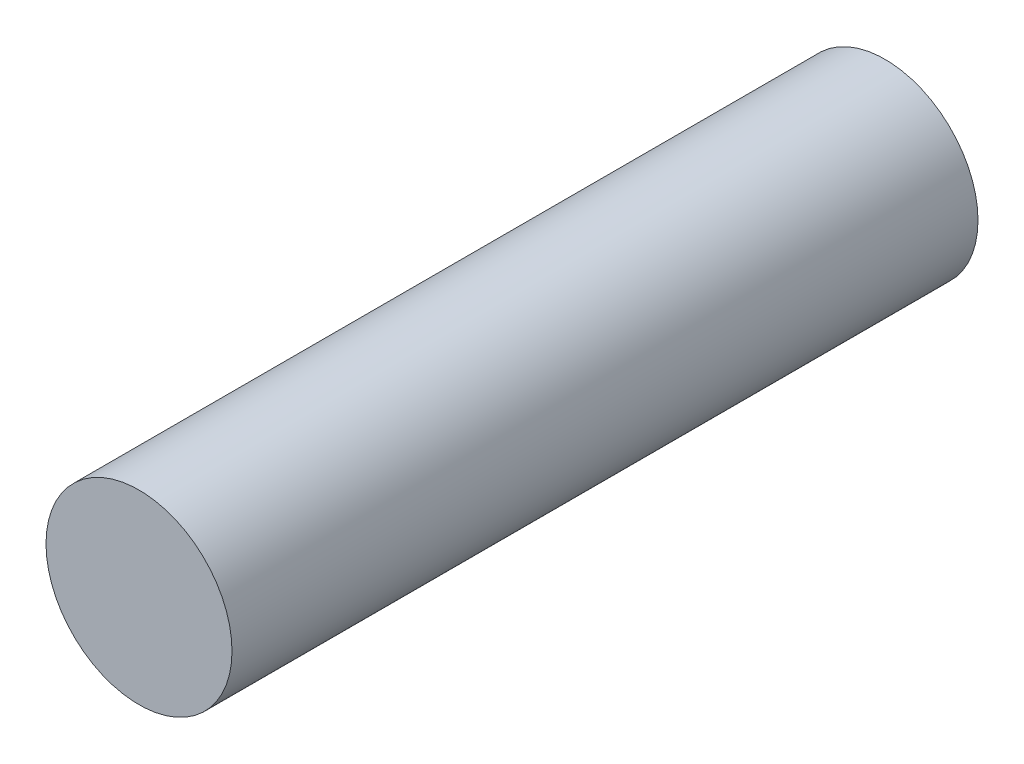
SolidWorks part; units mm, degrees
ref_plane "Front Plane" through (0, 0, 0) normal (0, 0, 1) x (1, 0, 0)
ref_plane "Top Plane" through (0, 0, 0) normal (0, 1, 0) x (1, 0, 0)
ref_plane "Right Plane" through (0, 0, 0) normal (1, 0, 0) x (0, 0, -1)
sketch "Sketch2" plane through (0, 0, 0) normal (0, 0, 1) x (1, 0, 0)
  circle A0 centre (0, 0) radius 2.3749
extrude "Boss-Extrude1" add sketch "Sketch2" along normal blind 19.05
